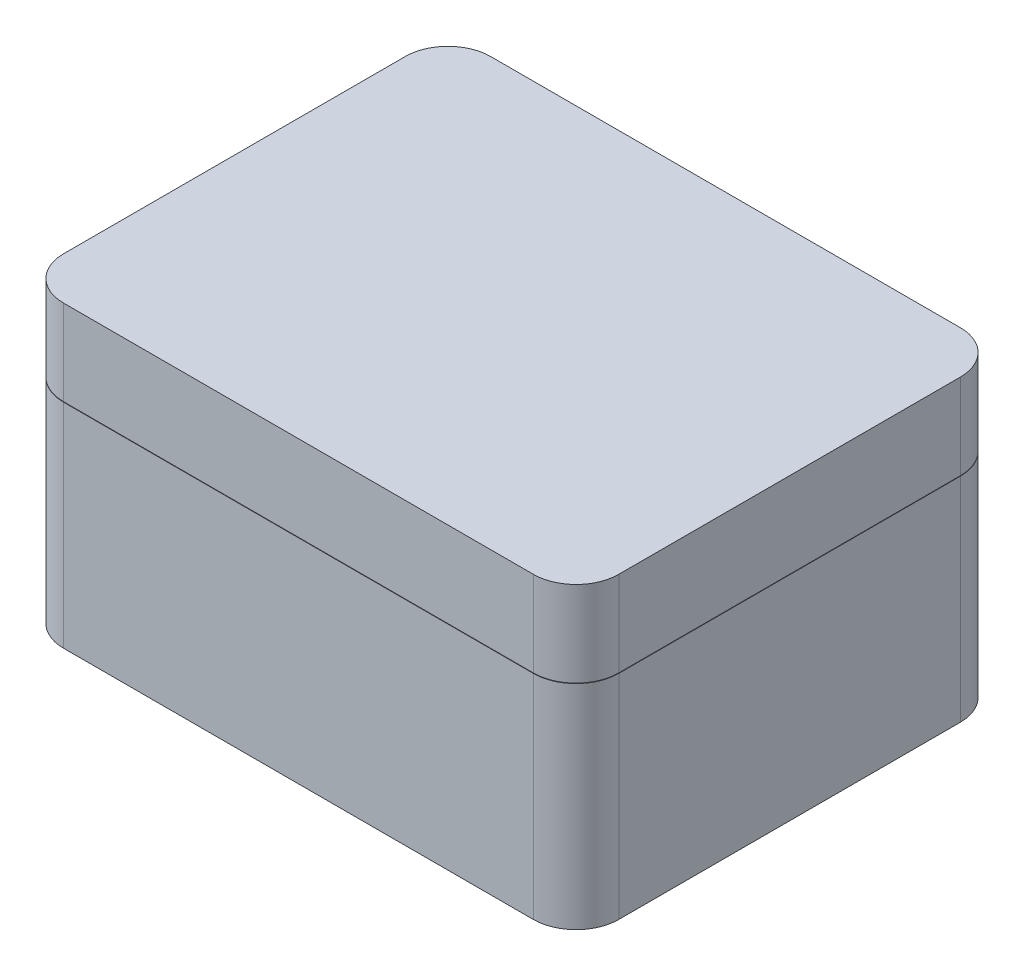
SolidWorks part; units mm, degrees
ref_plane "Front Plane" through (0, 0, 0) normal (0, 0, 1) x (1, 0, 0)
ref_plane "Top Plane" through (0, 0, 0) normal (0, 1, 0) x (1, 0, 0)
ref_plane "Right Plane" through (0, 0, 0) normal (1, 0, 0) x (0, 0, -1)
sketch "Sketch1" plane through (0, 0, 0) normal (0, 1, 0) x (1, 0, 0)
  line L1 (-32.5, -25) -> (32.5, -25)
  line L2 (-32.5, -25) -> (-32.5, 25)
  line L3 (-32.5, 25) -> (32.5, 25)
  line L4 (32.5, -25) -> (32.5, 25)
  line L5 (-32.5, -25) -> (32.5, 25) construction
  line L6 (-32.5, 25) -> (32.5, -25) construction
  point P0 (0, 0)
  dimension "D1" = 65
  dimension "D2" = 50
extrude "Boss-Extrude1" add sketch "Sketch1" along normal blind 35
fillet "Fillet2" radius 5 4 edges at (-32.5, 17.5, 25) (-32.5, 17.5, -25) (32.5, 17.5, -25) (32.5, 17.5, 25)
shell "Shell3" thickness 2
sketch "Sketch5" plane through (32.5, 0, 0) normal (1, 0, 0) x (0, 0, -1)
  line L0 (25, 35) -> (25, 0) construction
  line L1 (-25, 25) -> (25, 25)
  line L2 (-25, 25) -> (-25, 24.95)
  line L3 (-25, 24.95) -> (25, 24.95)
  line L4 (25, 25) -> (25, 24.95)
  line L5 (-25, 0) -> (-25, 35) construction
  line L6 (-20, 35) -> (20, 35) construction
  dimension "D1" = 10
  dimension "D2" = 0.05
extrude "Cut-Extrude1" cut sketch "Sketch5" against normal through all
sketch "Sketch6" plane through (0, 0, 0) normal (0, -1, 0) x (1, 0, 0)
  line L0 (-27.5, 25) -> (27.5, 25) construction
  line L1 (-32.5, -20) -> (-32.5, 20) construction
  line L2 (0, 25) -> (0, -25) construction
  line L3 (27.5, -25) -> (-27.5, -25) construction
  line L4 (-32.5, 0) -> (32.5, 0) construction
  line L5 (32.5, 20) -> (32.5, -20) construction
  circle A0 centre (-27.25, 19.75) radius 2
  circle A4 centre (25.25, -17.75) radius 2
  point P2 (-25.25, 19.75)
  point P4 (-27.25, 17.75)
  point P16 (27.2777, -19.4635)
  point P21 (24.8577, -25)
  dimension "D1" = 4
  dimension "D4" = 7.25
  dimension "D2" = 7.25
  dimension "D3" = 7.25
  dimension "D5" = 7.25
extrude "Cut-Extrude2" cut sketch "Sketch6" against normal up to next
